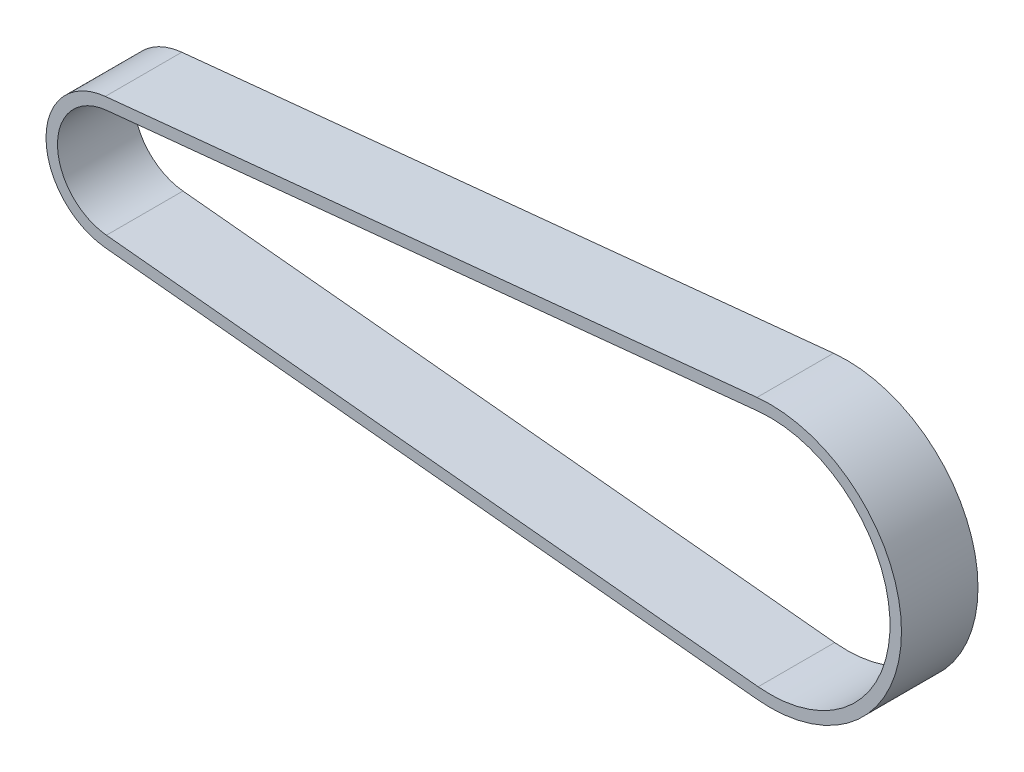
SolidWorks part; units mm, degrees
ref_plane "Front Plane" through (0, 0, 0) normal (0, 0, 1) x (1, 0, 0)
ref_plane "Top Plane" through (0, 0, 0) normal (0, 1, 0) x (1, 0, 0)
ref_plane "Right Plane" through (0, 0, 0) normal (1, 0, 0) x (0, 0, -1)
sketch "Sketch2" plane through (0, 0, 0) normal (0, 0, 1) x (1, 0, 0)
  line L0 (0, 0) -> (1, 0) construction
  line L1 (0, 0) -> (0, 1) construction
  line L2 (-1.0611, 10.6071) -> (126.6986, 23.3883)
  line L3 (126.6986, -23.3883) -> (-1.0611, -10.6071)
  line L4 (-1.2851, 12.8459) -> (126.4746, 25.6271)
  line L5 (126.4746, -25.6271) -> (-1.2851, -12.8459)
  line L6 (-2.25, -2.25) -> (-2.25, 1)
  line L7 (-2.25, -2.25) -> (1, -2.25)
  arc A0 (-1.0611, -10.6071) -> (-1.0611, 10.6071) centre (0, 0) cw
  arc A1 (126.6986, 23.3883) -> (126.6986, -23.3883) centre (129.0384, 0) cw
  arc A2 (126.4746, 25.6271) -> (126.4746, -25.6271) centre (129.0384, 0) cw
  arc A3 (-1.2851, -12.8459) -> (-1.2851, 12.8459) centre (0, 0) cw
  dimension "D1" = 2.25
extrude "Boss-Extrude1" add sketch "Sketch2" along normal blind 9 and the other way blind 6 contours A3 L5 A2 L4 L2 A1 L3 A0
